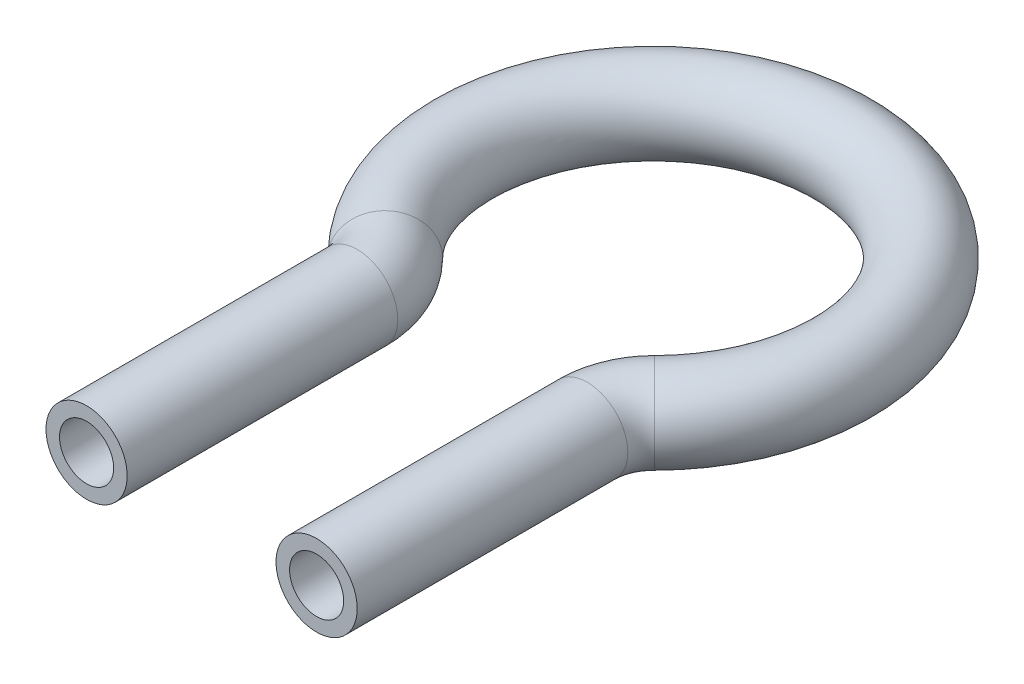
SolidWorks part; units mm, degrees
ref_plane "Front Plane" through (0, 0, 0) normal (0, 0, 1) x (1, 0, 0)
ref_plane "Top Plane" through (0, 0, 0) normal (0, 1, 0) x (1, 0, 0)
ref_plane "Right Plane" through (0, 0, 0) normal (1, 0, 0) x (0, 0, -1)
sketch "Sketch1" plane through (0, 0, 0) normal (0, 1, 0) x (1, 0, 0)
  line L1 (8.5, -13.3697) -> (8.5, -33.3697)
  line L2 (-8.5, -13.3697) -> (-8.5, -33.3697)
  arc A0 (-9.9474, -9.8514) -> (9.9474, -9.8514) centre (0, 0) cw
  arc A1 (9.9474, -9.8514) -> (8.5, -13.3697) centre (13.5, -13.3697) ccw
  arc A2 (-9.9474, -9.8514) -> (-8.5, -13.3697) centre (-13.5, -13.3697) cw
  dimension "D1" = 14
  dimension "D3" = 5
  dimension "D4" = 5
  dimension "D2" = 20
  dimension "D5" = 17
ref_plane "Plane1" through (-8.5, 0, 33.3697) normal (0, 0, -1) x (-1, 0, 0)
sketch "Sketch2" plane through (-8.5, 0, 33.3697) normal (0, 0, -1) x (-1, 0, 0)
  circle A0 centre (0, 0) radius 3
  circle A1 centre (0, 0) radius 2
  dimension "D1" = 6
  dimension "D2" = 4
sweep "Sweep1" add profiles "Sketch2" path "Sketch1"
